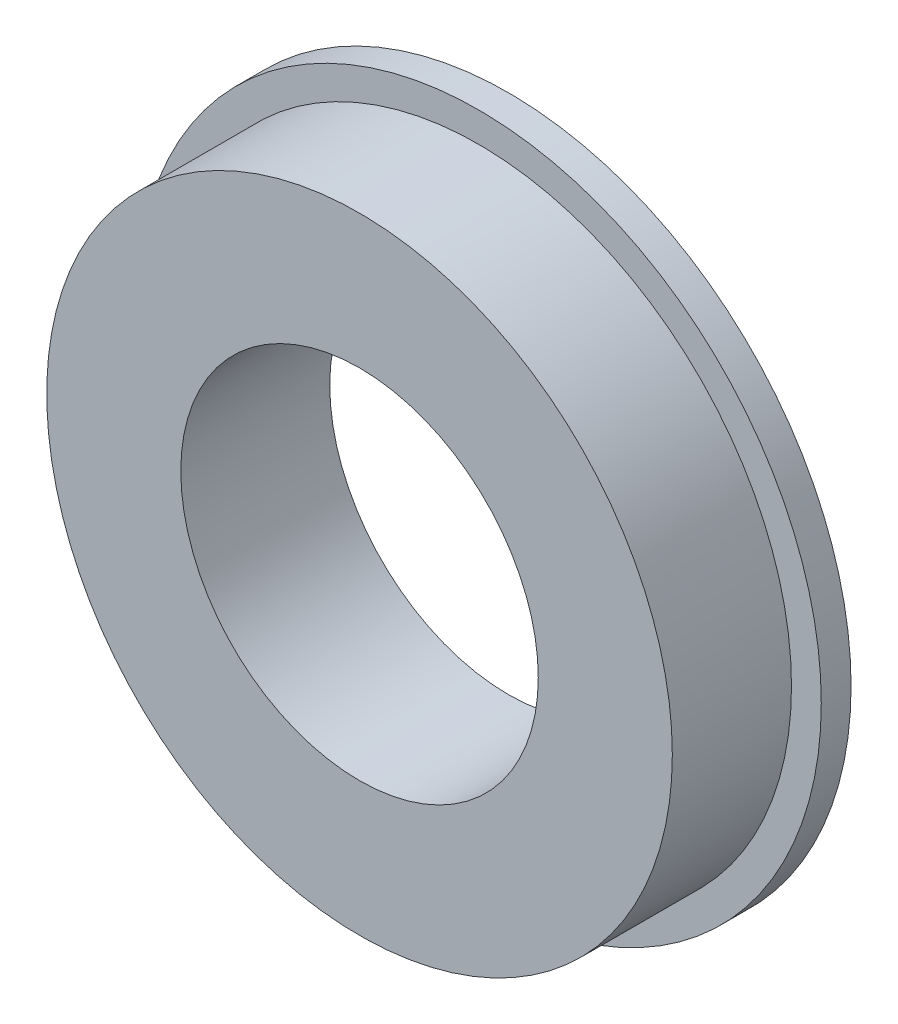
SolidWorks part; units mm, degrees
ref_plane "前视基准面" through (0, 0, 0) normal (0, 0, 1) x (1, 0, 0)
ref_plane "上视基准面" through (0, 0, 0) normal (0, 1, 0) x (1, 0, 0)
ref_plane "右视基准面" through (0, 0, 0) normal (1, 0, 0) x (0, 0, -1)
sketch "草图1" plane through (0, 0, 0) normal (0, 0, 1) x (1, 0, 0)
  circle A0 centre (0, 0) radius 11.5
  dimension "D1" = 23
extrude "凸台-拉伸1" add sketch "草图1" along normal blind 1
sketch "草图2" plane through (0, 0, 1) normal (0, 0, 1) x (1, 0, 0)
  circle A0 centre (0, 0) radius 10.5
  dimension "D1" = 21
extrude "凸台-拉伸2" add sketch "草图2" along normal blind 4
sketch "草图3" plane through (0, 0, 5) normal (0, 0, 1) x (1, 0, 0)
  circle A0 centre (0, 0) radius 6
  dimension "D1" = 12
extrude "切除-拉伸1" cut sketch "草图3" against normal through all
